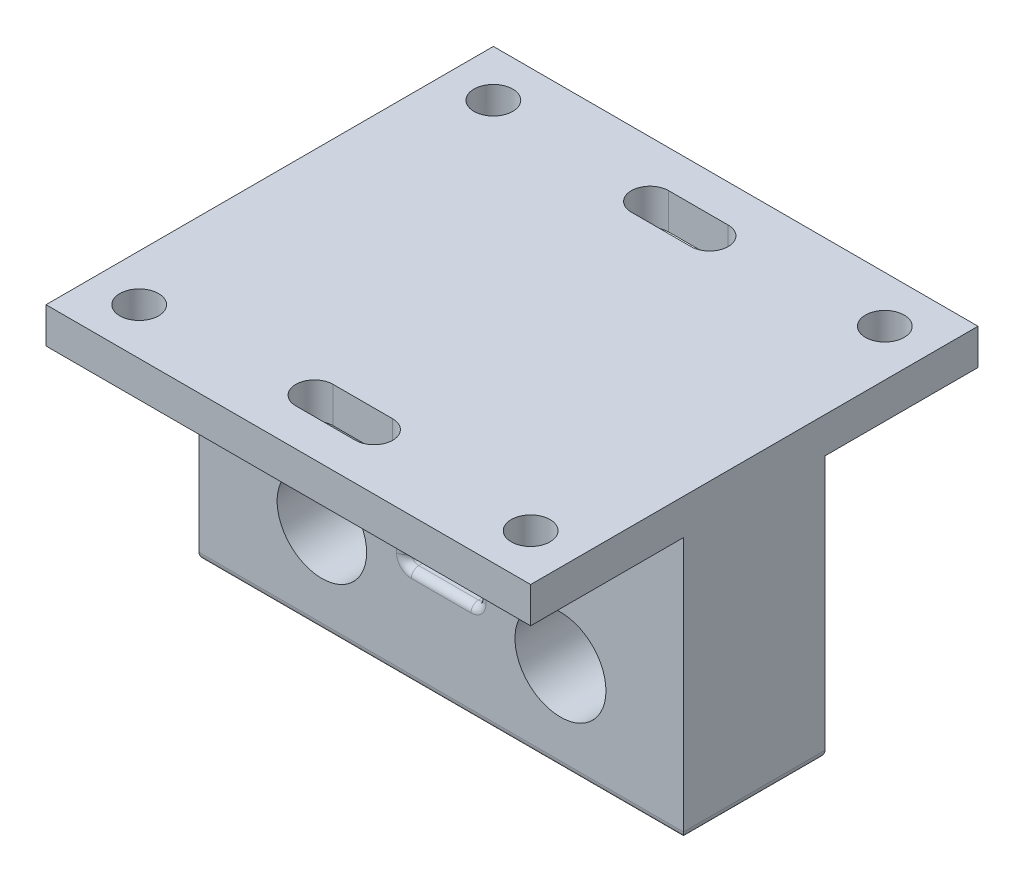
SolidWorks part; units mm, degrees
ref_plane "Front Plane" through (0, 0, 0) normal (0, 0, 1) x (1, 0, 0)
ref_plane "Top Plane" through (0, 0, 0) normal (0, 1, 0) x (1, 0, 0)
ref_plane "Right Plane" through (0, 0, 0) normal (1, 0, 0) x (0, 0, -1)
sketch "Sketch1" plane through (0, 0, 0) normal (0, 0, 1) x (1, 0, 0)
  line L0 (-2, 0) -> (30, 0) construction
  line L1 (-18.5, -12.2) -> (46.5, -12.2)
  line L2 (-18.5, -12.2) -> (-18.5, 27.8)
  line L3 (-18.5, 27.8) -> (46.5, 27.8)
  line L4 (46.5, 27.8) -> (46.5, -12.2)
  circle A0 centre (-2, 0) radius 6
  circle A1 centre (30, 0) radius 6.1
  point P7 (14, -12.2)
  point P8 (14, 0)
  dimension "D1" = 12
  dimension "D3" = 12.2
  dimension "D5" = 12.2
  dimension "D2" = 32
  dimension "D4" = 40
  dimension "D6" = 65
extrude "Boss-Extrude1" add sketch "Sketch1" against normal blind 19
ref_plane "Plane1" through (0, 0, -9.5) normal (0, 0, 1) x (1, 0, 0)
sketch "Sketch4" plane through (0, 0, -9.5) normal (0, 0, 1) x (1, 0, 0)
  line L0 (-18.5, 27.8) -> (46.5, 27.8)
  line L1 (46.5, 27.8) -> (46.5, 13)
  line L2 (46.5, -12.2) -> (46.5, 27.8) construction
  line L3 (46.5, 13) -> (-18.5, 13)
  line L4 (-18.5, 27.8) -> (-18.5, -12.2) construction
  line L5 (-18.5, 13) -> (-18.5, 27.8)
extrude "Boss-Extrude2" add sketch "Sketch4" along normal mid plane 70
sketch "Sketch6" plane through (0, 0, 0) normal (0, 0, 1) x (1, 0, 0)
  line L0 (14, 13) -> (14, -12.2) construction
  line L1 (-18.5, 13) -> (46.5, 13) construction
  line L2 (-18.5, -12.2) -> (46.5, -12.2) construction
  line L3 (9, 13) -> (19, 13)
  line L4 (9, 13) -> (9, 1)
  line L5 (19, 1) -> (19, 13)
  line L6 (9, 1) -> (19, 1)
  point P8 (14, 13)
  dimension "D1" = 10
  dimension "D2" = 12
extrude "Cut-Extrude1" cut sketch "Sketch6" against normal through all
sketch "Sketch7" plane through (-18.5, 0, 0) normal (-1, 0, 0) x (0, 0, 1)
  line L0 (-44.5, 27.8) -> (-44.5, 13) construction
  line L1 (-9.5, 27.8) -> (-9.5, -12.2) construction
  line L2 (-44.5, 27.8) -> (25.5, 27.8) construction
  line L3 (-19, -12.2) -> (0, -12.2) construction
  line L4 (-44.5, 16.5761) -> (-44.5, 13)
  line L5 (-44.5, 13) -> (-19, 13)
  line L6 (0, 13) -> (25.5, 13)
  line L7 (25.5, 13) -> (25.5, 16.5761)
  line L8 (25.5, 27.8) -> (25.5, 13) construction
  arc A0 (-44.5, 16.5761) -> (-19, 13) centre (-20.5063, 94.9639) ccw
  arc A1 (25.5, 16.5761) -> (0, 13) centre (1.5063, 94.9639) cw
  line M2 (-44.5, 13) -> (-19, 13)
  line M7 (25.5, 13) -> (25.5, 27.8)
  line M9 (-44.5, 27.8) -> (-44.5, 13)
extrude "Cut-Extrude2" [suppressed] cut sketch "Sketch7" against normal through all contours A0 M9 M2 | A1 L6 M7
sketch "Sketch8" plane through (0, 27.8, 0) normal (0, 1, 0) x (1, 0, 0)
  line L0 (-18.3079, 9.5) -> (18.3079, 9.5) construction
  line L2 (46.5, -25.5) -> (-18.5, -25.5) construction
  line L3 (18, 32) -> (10, 32) construction
  line L4 (18, 29.5) -> (10, 29.5)
  line L5 (18, 34.5) -> (10, 34.5)
  line L6 (18, -13) -> (10, -13) construction
  line L7 (18, -10.5) -> (10, -10.5)
  line L8 (18, -15.5) -> (10, -15.5)
  arc A0 (18, 29.5) -> (18, 34.5) centre (18, 32) ccw
  arc A1 (10, 34.5) -> (10, 29.5) centre (10, 32) ccw
  arc A2 (18, -10.5) -> (18, -15.5) centre (18, -13) cw
  arc A3 (10, -15.5) -> (10, -10.5) centre (10, -13) cw
  point P8 (14, 32)
  point P16 (14, -13)
  dimension "D2" = 2.5
  dimension "D3" = 12.5
  dimension "D1" = 8
extrude "Cut-Extrude3" cut sketch "Sketch8" against normal through all
fillet "Fillet1" radius 1 12 edges at (19, 7, -19) (9, 7, -19) (9, 7, 0) (19, 7, 0) (46.5, -12.2, -9.5) (14, -12.2, -19) (-18.5, -12.2, -9.5) (14, -12.2, 0) (14, 1, -19) (14, 1, 0) (9, 1, -9.5) (19, 1, -9.5)
sketch "Sketch9" plane through (0, 0, 25.5) normal (0, 0, 1) x (1, 0, 0)
  line L4 (-18.5, 27.8) -> (-18.5, 13)
  line L5 (-18.5, 13) -> (46.5, 13)
  line L6 (46.5, 13) -> (46.5, 27.8)
  line L7 (46.5, 27.8) -> (-18.5, 27.8)
  line L8 (-18.5, 27.8) -> (-18.5, 13)
  line L9 (-18.5, 13) -> (46.5, 13)
  line L10 (46.5, 13) -> (46.5, 27.8)
  line L11 (46.5, 27.8) -> (-18.5, 27.8)
  dimension "D1" = 0
extrude "Cut-Extrude4" cut sketch "Sketch9" against normal blind 5
sketch "Sketch10" plane through (0, 0, -44.5) normal (0, 0, -1) x (-1, 0, 0)
  line L4 (18.5, 13) -> (18.5, 27.8)
  line L5 (18.5, 27.8) -> (-46.5, 27.8)
  line L6 (-46.5, 27.8) -> (-46.5, 13)
  line L7 (-46.5, 13) -> (18.5, 13)
  line L8 (18.5, 13) -> (18.5, 27.8)
  line L9 (18.5, 27.8) -> (-46.5, 27.8)
  line L10 (-46.5, 27.8) -> (-46.5, 13)
  line L11 (-46.5, 13) -> (18.5, 13)
  dimension "D1" = 0
extrude "Cut-Extrude5" cut sketch "Sketch10" against normal blind 5
sketch "Sketch11" plane through (0, 27.8, 0) normal (0, 1, 0) x (1, 0, 0)
  line L0 (46.5, -20.5) -> (40.25, -20.5) construction
  line L1 (46.5, -20.5) -> (-18.5, -20.5) construction
  line L2 (40.25, -20.5) -> (40.25, -14.25) construction
  line L3 (-18.5, 9.5) -> (46.5, 9.5) construction
  line L4 (-18.5, 39.5) -> (-18.5, -20.5) construction
  line L5 (46.5, 39.5) -> (46.5, -20.5) construction
  line L6 (14, -20.5) -> (14, 39.5) construction
  line L7 (-18.5, 39.5) -> (46.5, 39.5) construction
  circle A0 centre (40.25, -14.25) radius 2.6
  circle A1 centre (40.25, 33.25) radius 2.6
  circle A2 centre (-12.25, 33.25) radius 2.6
  circle A3 centre (-12.25, -14.25) radius 2.6
  dimension "D1" = 5.2
extrude "Cut-Extrude6" cut sketch "Sketch11" against normal through all
sketch "Sketch12" plane through (0, 13, 0) normal (0, -1, 0) x (1, 0, 0)
  line L12 (-18.5, -39.5) -> (46.5, -39.5)
  line L13 (46.5, -39.5) -> (46.5, -19)
  line L14 (46.5, -19) -> (20, -19)
  line L15 (19, -18) -> (19, -1)
  line L16 (20, 0) -> (46.5, 0)
  line L17 (46.5, 0) -> (46.5, 20.5)
  line L18 (46.5, 20.5) -> (-18.5, 20.5)
  line L19 (-18.5, 20.5) -> (-18.5, 0)
  line L20 (-18.5, 0) -> (8, 0)
  line L21 (9, -1) -> (9, -18)
  line L22 (8, -19) -> (-18.5, -19)
  line L23 (-18.5, -19) -> (-18.5, -39.5)
  line L24 (-18.5, -39.5) -> (46.5, -39.5)
  line L25 (46.5, -39.5) -> (46.5, -19)
  line L26 (46.5, -19) -> (20, -19)
  line L27 (19, -18) -> (19, -1)
  line L28 (20, 0) -> (46.5, 0)
  line L29 (46.5, 0) -> (46.5, 20.5)
  line L30 (46.5, 20.5) -> (-18.5, 20.5)
  line L31 (-18.5, 20.5) -> (-18.5, 0)
  line L32 (-18.5, 0) -> (8, 0)
  line L33 (9, -1) -> (9, -18)
  line L34 (8, -19) -> (-18.5, -19)
  line L35 (-18.5, -19) -> (-18.5, -39.5)
  arc A4 (19, -18) -> (20, -19) centre (20, -18) ccw
  arc A5 (20, 0) -> (19, -1) centre (20, -1) ccw
  arc A6 (9, -1) -> (8, 0) centre (8, -1) ccw
  arc A7 (8, -19) -> (9, -18) centre (8, -18) ccw
  arc A8 (19, -18) -> (20, -19) centre (20, -18) ccw
  arc A9 (20, 0) -> (19, -1) centre (20, -1) ccw
  arc A10 (9, -1) -> (8, 0) centre (8, -1) ccw
  arc A11 (8, -19) -> (9, -18) centre (8, -18) ccw
  dimension "D1" = 0
extrude "Cut-Extrude7" cut sketch "Sketch12" against normal blind 10
